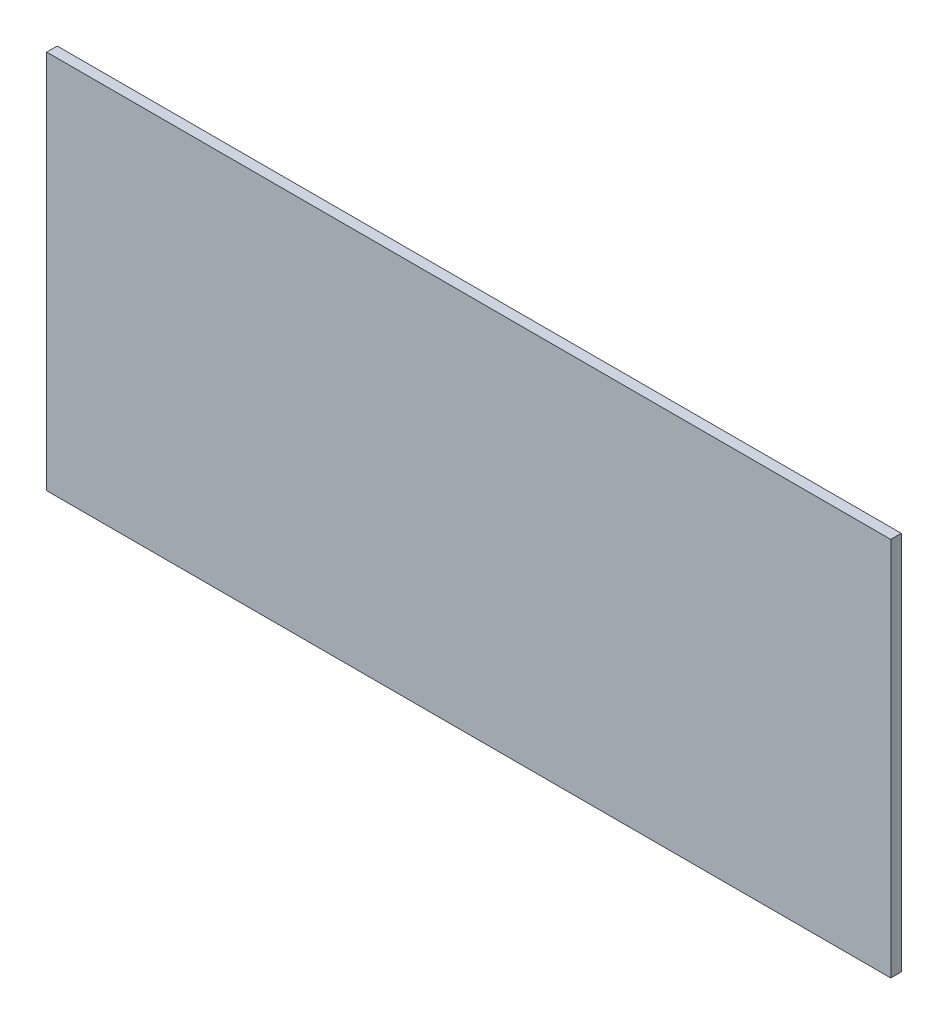
SolidWorks part; units mm, degrees
ref_plane "Front Plane" through (0, 0, 0) normal (0, 0, 1) x (1, 0, 0)
ref_plane "Top Plane" through (0, 0, 0) normal (0, 1, 0) x (1, 0, 0)
ref_plane "Right Plane" through (0, 0, 0) normal (1, 0, 0) x (0, 0, -1)
sketch "Sketch1" plane through (0, 0, 0) normal (0, 0, 1) x (1, 0, 0)
  line L1 (0, 0) -> (2032, 0)
  line L2 (0, 0) -> (0, -914.4)
  line L3 (0, -914.4) -> (2032, -914.4)
  line L4 (2032, 0) -> (2032, -914.4)
  dimension "D1" = 914.4
  dimension "D2" = 2032
extrude "Boss-Extrude1" add sketch "Sketch1" along normal blind 25.4
ref_plane "Plane1" through (0, 0, 25.4) normal (0, -1, 0) x (-1, 0, 0)
